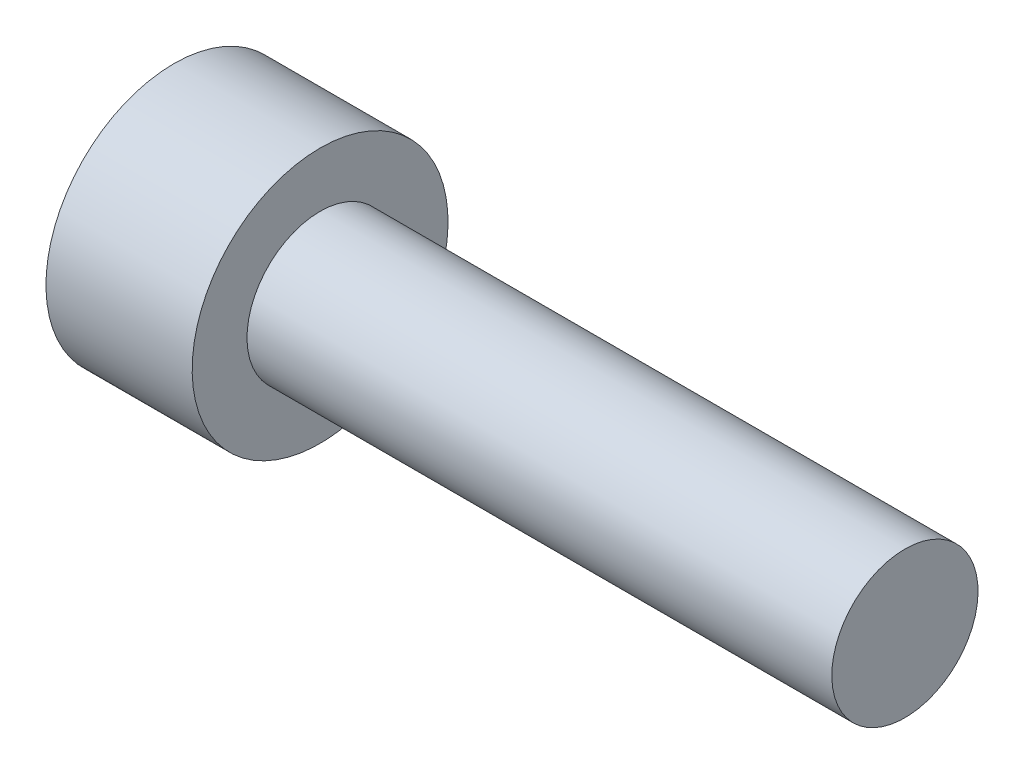
SolidWorks part; units mm, degrees
ref_plane "Płaszczyzna przednia" through (0, 0, 0) normal (0, 0, 1) x (1, 0, 0)
ref_plane "Płaszczyzna górna" through (0, 0, 0) normal (0, 1, 0) x (1, 0, 0)
ref_plane "Płaszczyzna prawa" through (0, 0, 0) normal (1, 0, 0) x (0, 0, -1)
sketch "Szkic1" plane through (0, 0, 0) normal (0, 0, 1) x (1, 0, 0)
  line L0 (0, 0) -> (0, 3.5)
  line L1 (0, 3.5) -> (4, 3.5)
  line L2 (4, 3.5) -> (4, 2)
  line L3 (4, 2) -> (20, 2)
  line L4 (20, 2) -> (20, 0)
  line L5 (20, 0) -> (0, 0)
  dimension "D1" = 4
  dimension "D2" = 16
  dimension "D3" = 2
  dimension "D4" = 3.5
revolve "Obrót1" add sketch "Szkic1" angle 360 about L5
cosmetic thread "Oznaczenie gwintu1" parameters "D2"=3.22
sketch "Szkic2" plane through (0, 0, 0) normal (-1, 0, 0) x (0, 0, 1)
  line L0 (-0.866, -1.5) -> (0.866, -1.5)
  line L7 (0.866, -1.5) -> (1.7321, 0)
  line L8 (1.7321, 0) -> (0.866, 1.5)
  line L9 (0.866, 1.5) -> (-0.866, 1.5)
  line L10 (-0.866, 1.5) -> (-1.7321, 0)
  line L11 (-1.7321, 0) -> (-0.866, -1.5)
  circle A0 centre (0, 0) radius 1.7321 construction
  dimension "D1" = 3
extrude "Wytnij-wyciągnięcie1" cut sketch "Szkic2" against normal blind 2
